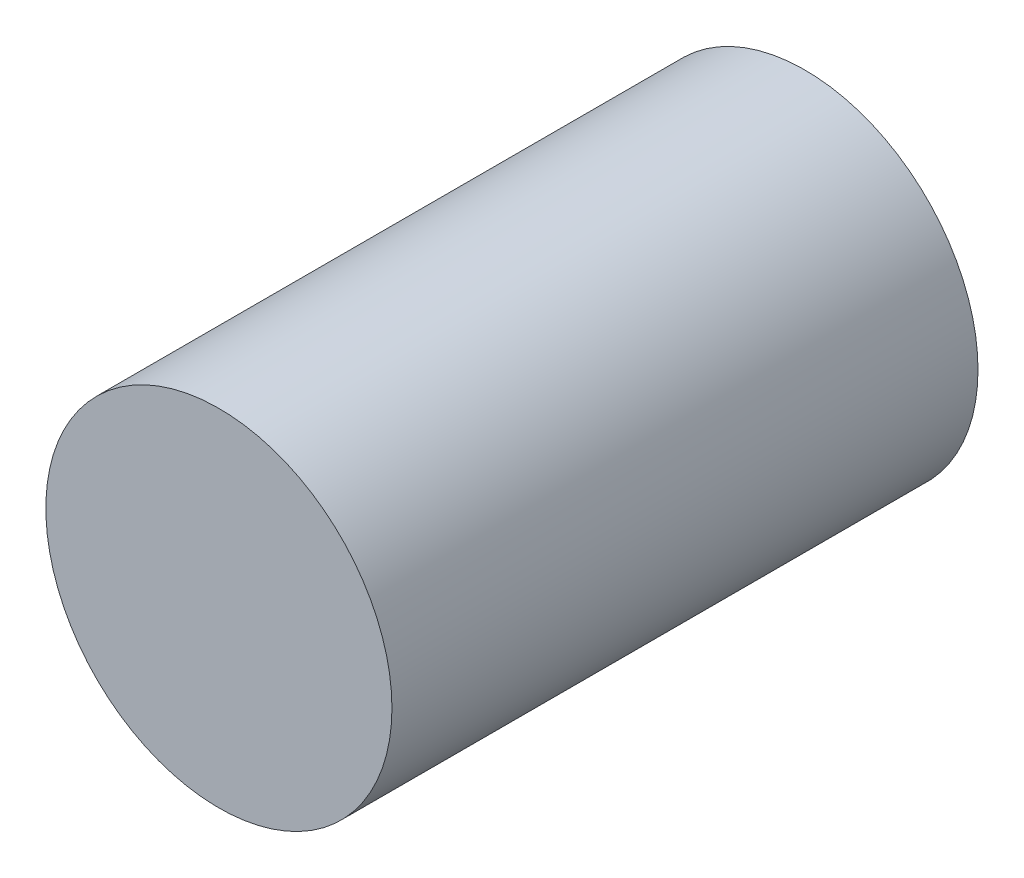
SolidWorks part; units mm, degrees
ref_plane "Front Plane" through (0, 0, 0) normal (0, 0, 1) x (1, 0, 0)
ref_plane "Top Plane" through (0, 0, 0) normal (0, 1, 0) x (1, 0, 0)
ref_plane "Right Plane" through (0, 0, 0) normal (1, 0, 0) x (0, 0, -1)
sketch "Sketch1" plane through (0, 0, 0) normal (0, 0, 1) x (1, 0, 0)
  circle A0 centre (0, 0) radius 7.5
  dimension "D1" = 15
extrude "Boss-Extrude1" add sketch "Sketch1" along normal blind 25.4
